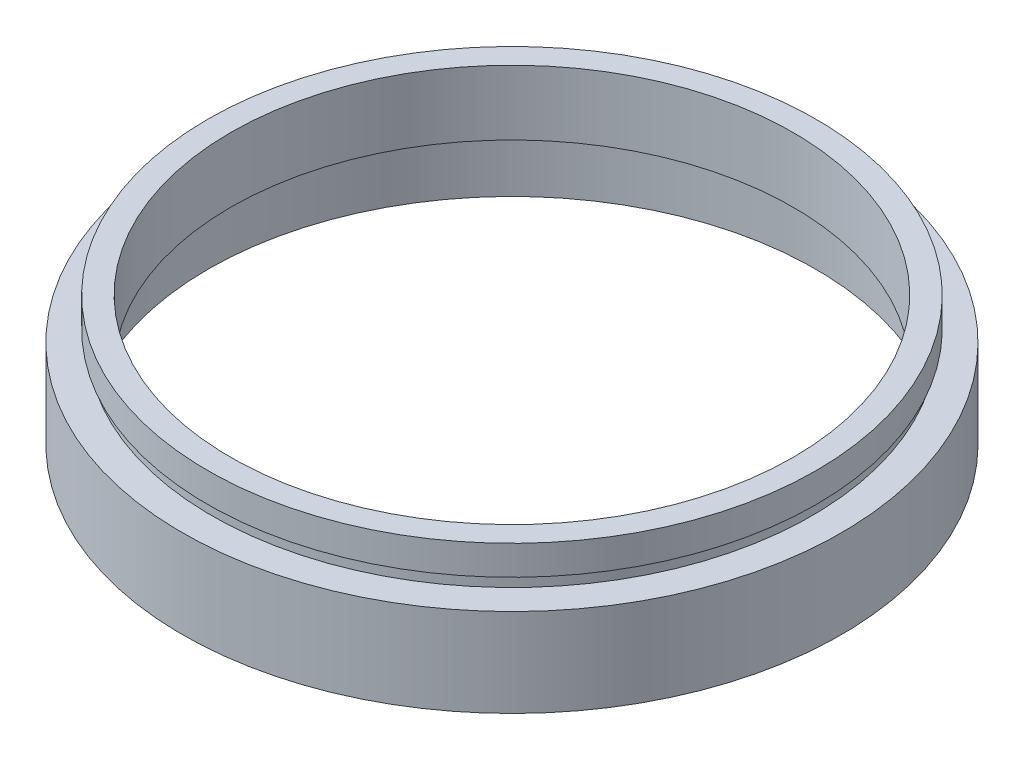
SolidWorks part; units mm, degrees
ref_plane "前视基准面" through (0, 0, 0) normal (0, 0, 1) x (1, 0, 0)
ref_plane "上视基准面" through (0, 0, 0) normal (0, 1, 0) x (1, 0, 0)
ref_plane "右视基准面" through (0, 0, 0) normal (1, 0, 0) x (0, 0, -1)
sketch "草图1" plane through (0, 0, 0) normal (0, 0, 1) x (1, 0, 0)
  line L0 (0, 16.886) -> (0, -24.4878) construction
  line L1 (25.8, 0) -> (25.8, 4.5)
  line L2 (23.9, 5.5) -> (26.1, 5.5)
  line L3 (23.9, 5.5) -> (23.9, 11)
  line L4 (23.9, 11) -> (25.85, 11)
  line L5 (25.85, 11) -> (25.85, 8.5)
  line L6 (25.85, 8.5) -> (25.5, 8.5)
  line L7 (25.5, 8.5) -> (25.5, 7.5)
  line L8 (25.5, 7.5) -> (28, 7.5)
  line L9 (28, 7.5) -> (28, 0)
  line L10 (28, 0) -> (25.8, 0)
  line L11 (25.8, 4.5) -> (26.1, 4.5)
  line L12 (26.1, 4.5) -> (26.1, 5.5)
  line L13 (0, 0) -> (3.4668, 0) construction
  point P4 (26.9, 0)
  dimension "D1" = 23.9
  dimension "D2" = 25.85
  dimension "D3" = 25.5
  dimension "D4" = 25.8
  dimension "D5" = 26.1
  dimension "D6" = 28
  dimension "D7" = 11
  dimension "D8" = 7.5
  dimension "D9" = 1
  dimension "D10" = 4.5
  dimension "D11" = 1
revolve "旋转1" add sketch "草图1" angle 360 about L0
cosmetic thread "装饰螺纹线1"
cosmetic thread "装饰螺纹线2"
cosmetic thread "装饰螺纹线3"
